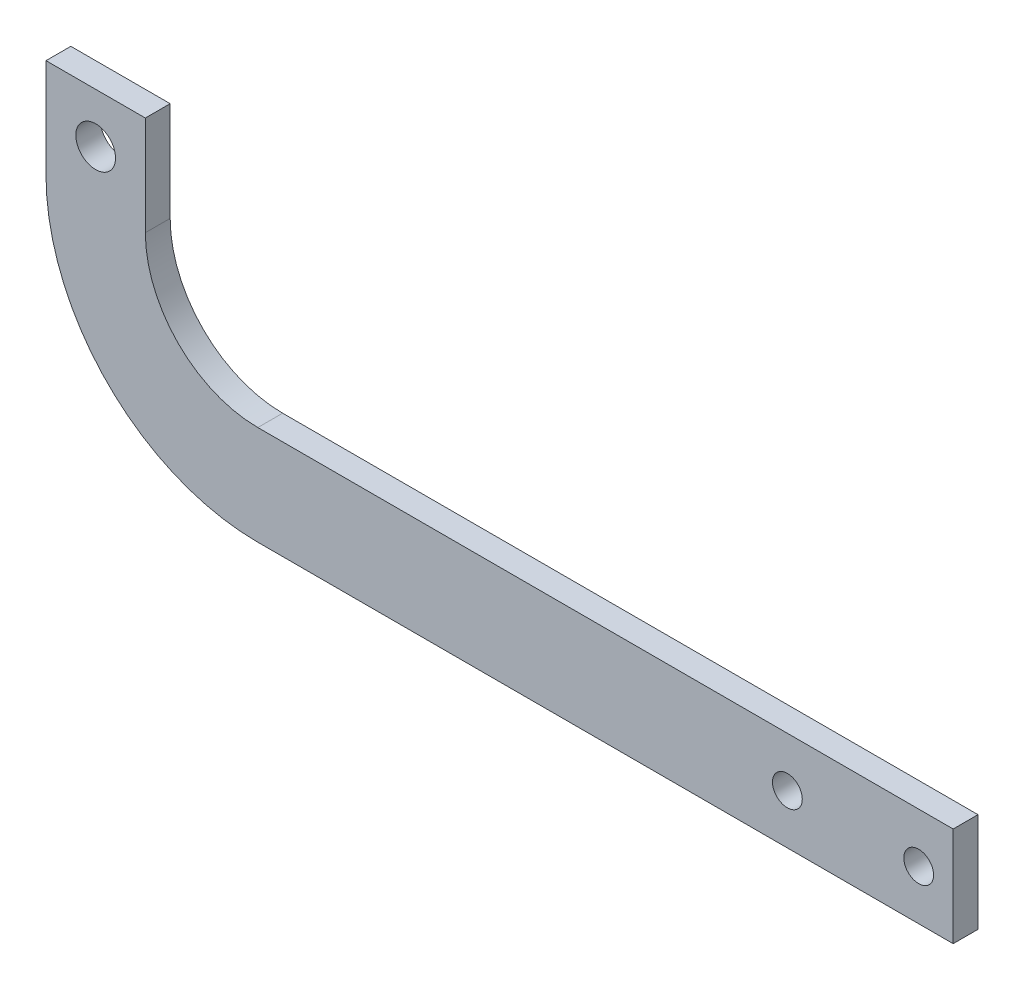
SolidWorks part; units mm, degrees
ref_plane "Plan de face" through (0, 0, 0) normal (0, 0, 1) x (1, 0, 0)
ref_plane "Plan de dessus" through (0, 0, 0) normal (0, 1, 0) x (1, 0, 0)
ref_plane "Plan de droite" through (0, 0, 0) normal (1, 0, 0) x (0, 0, -1)
sketch "Esquisse1" plane through (0, 0, 0) normal (0, 0, 1) x (1, 0, 0)
  line L1 (0, 0) -> (70, 0)
  line L2 (-21.3238, 21.3238) -> (-21.3238, 31.3238)
  line L3 (0, 10) -> (70, 10)
  line L4 (70, 0) -> (70, 10)
  line L5 (-21.3238, 31.3238) -> (-11.3238, 31.3238)
  line L6 (-11.3238, 31.3238) -> (-11.3238, 21.3238)
  arc A0 (-21.3238, 21.3238) -> (0, 0) centre (0, 21.3238) ccw
  arc A1 (-11.3238, 21.3238) -> (0, 10) centre (0, 21.3238) ccw
  circle A2 centre (-16.3238, 26.3238) radius 2
  circle A3 centre (66.53, 5) radius 1.5
  circle A4 centre (53.31, 5) radius 1.5
  dimension "D5" = 4
  dimension "D7" = 3
  dimension "D8" = 3
  dimension "D14" = 10
  dimension "D1" = 70
  dimension "D2" = 10
  dimension "D3" = 10
  dimension "D4" = 5
  dimension "D6" = 5
  dimension "D9" = 3.47
  dimension "D10" = 13.22
  dimension "D11" = 5
  dimension "D12" = 5
  dimension "D13" = 10
extrude "Boss.-Extru.1" add sketch "Esquisse1" along normal blind 2.5
